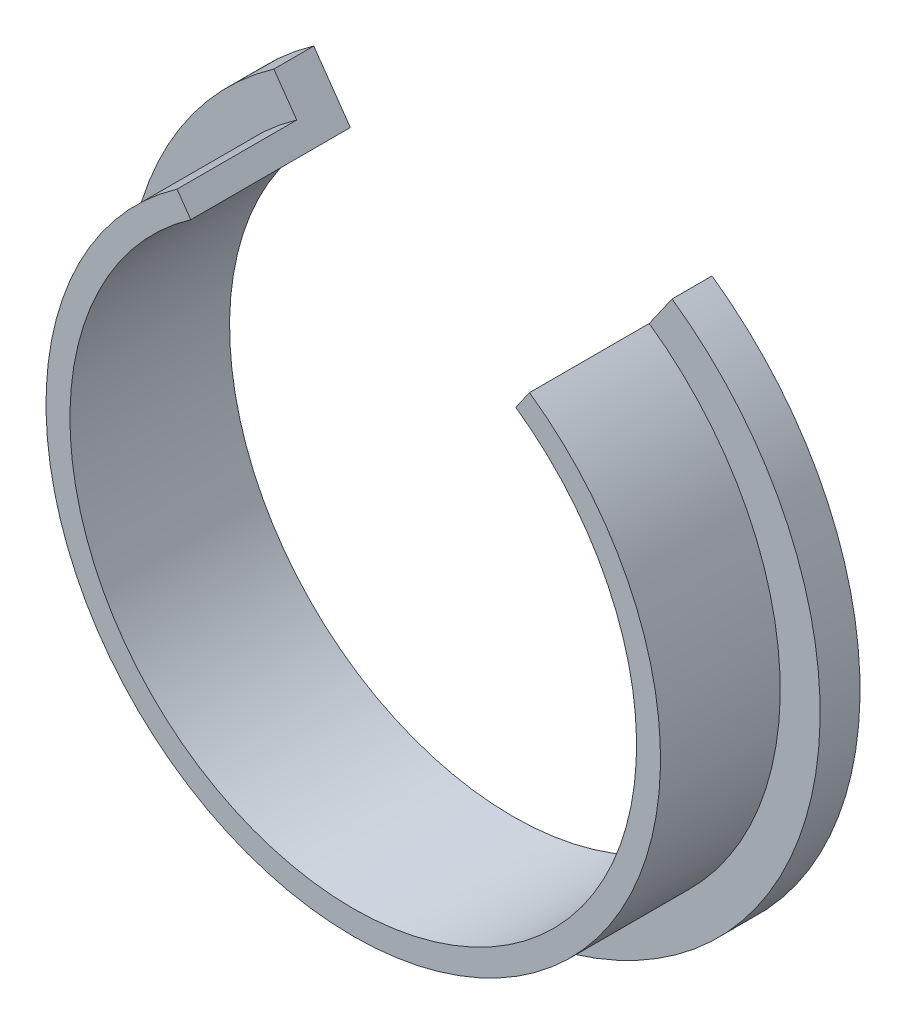
SolidWorks part; units mm, degrees
material "ABS"
ref_plane "Plano frontal" through (0, 0, 0) normal (0, 0, 1) x (1, 0, 0)
ref_plane "Plano superior" through (0, 0, 0) normal (0, 1, 0) x (1, 0, 0)
ref_plane "Plano direito" through (0, 0, 0) normal (1, 0, 0) x (0, 0, -1)
sketch "Esboço1" plane through (0, 0, 0) normal (0, 0, 1) x (1, 0, 0)
  circle A0 centre (0, 0) radius 43.5
  dimension "D1" = 87
extrude "Ressalto-extrusão1" add sketch "Esboço1" along normal blind 5
sketch "Esboço2" plane through (0, 0, 5) normal (0, 0, 1) x (1, 0, 0)
  circle A0 centre (0, 0) radius 38.5
  dimension "D1" = 77
extrude "Ressalto-extrusão2" add sketch "Esboço2" along normal blind 15
sketch "Esboço3" plane through (0, 0, 20) normal (0, 0, 1) x (1, 0, 0)
  circle A0 centre (0, 0) radius 35.5
  dimension "D1" = 71
extrude "Corte-extrusão1" cut sketch "Esboço3" against normal through all
sketch "Esboço4" plane through (0, 0, 0) normal (0, 0, -1) x (-1, 0, 0)
  line L0 (0, -50.756) -> (0, 52.7788) construction
  line L1 (-72.6878, 0) -> (72.1533, 0) construction
  line L5 (0, 0) -> (24.9506, 35.6331)
  line L6 (0, 0) -> (-24.9506, 35.6331)
  arc A4 (24.9506, 35.6331) -> (-24.9506, 35.6331) centre (0, 0) ccw
  dimension "D1" = 35
extrude "Corte-extrusão2" cut sketch "Esboço4" against normal through all
